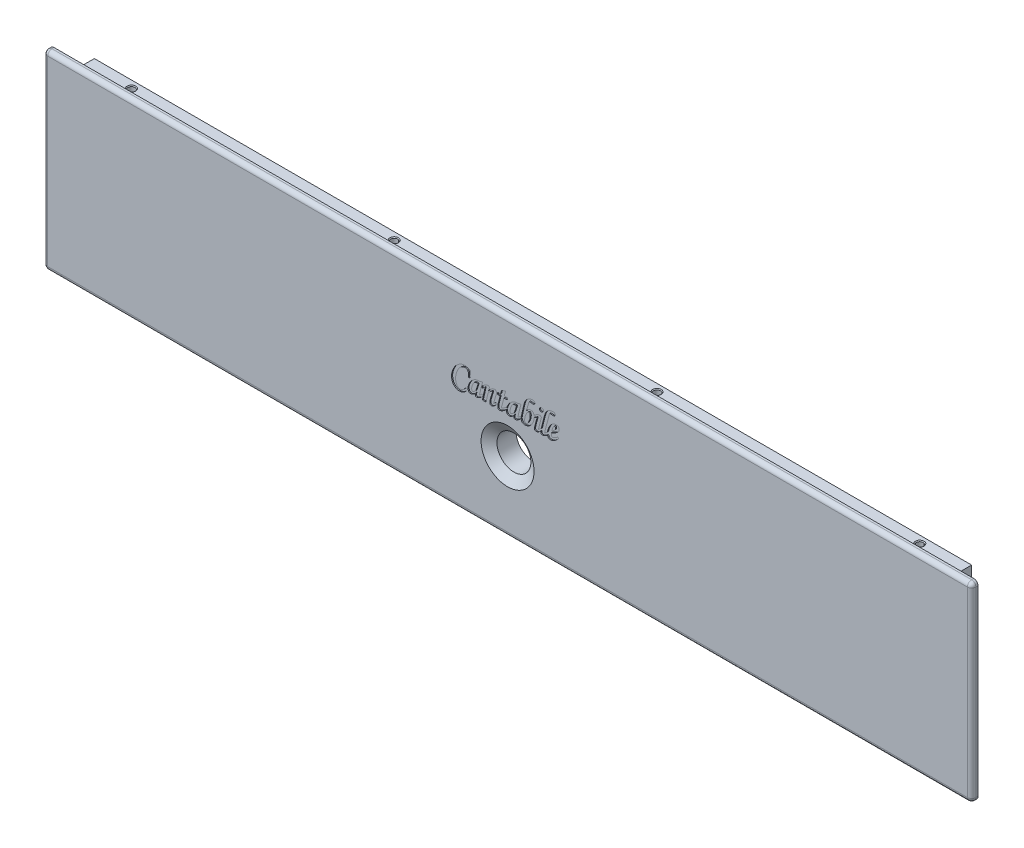
SolidWorks part; units mm, degrees
material "3.3523 (EN-AW 5052)"
ref_plane "前基準面" through (0, 0, 0) normal (0, 0, 1) x (1, 0, 0)
ref_plane "上基準面" through (0, 0, 0) normal (0, 1, 0) x (1, 0, 0)
ref_plane "右基準面" through (0, 0, 0) normal (1, 0, 0) x (0, 0, -1)
sketch "草圖1" plane through (0, 0, 0) normal (0, 0, 1) x (1, 0, 0)
  line L1 (0, 0) -> (438, 0)
  line L2 (0, 0) -> (0, 90)
  line L3 (0, 90) -> (438, 90)
  line L4 (438, 0) -> (438, 90)
  dimension "D1" = 438
  dimension "D2" = 90
extrude "填料-伸長1" add sketch "草圖1" along normal blind 12
sketch "草圖3" plane through (438, 0, 0) normal (1, 0, 0) x (0, 0, -1)
  line L1 (0, 90) -> (-9, 90)
  line L2 (0, 90) -> (0, 86)
  line L3 (0, 86) -> (-9, 86)
  line L4 (-9, 90) -> (-9, 86)
  line L5 (0, 0) -> (-9, 0)
  line L6 (0, 0) -> (0, 4)
  line L7 (0, 4) -> (-9, 4)
  line L8 (-9, 0) -> (-9, 4)
  dimension "D1" = 4
  dimension "D2" = 9
  dimension "D3" = 9
  dimension "D4" = 4
extrude "除料-伸長1" cut sketch "草圖3" against normal through all
hole_wizard "M1.6 錐坑平頭螺釘的錐孔1" positions "草圖9" profile "草圖10" countersink size "M1.6" standard "ISO" end condition through all
sketch "草圖9" plane through (0, 0, 12) normal (0, 0, 1) x (1, 0, 0)
  line L0 (438, 0) -> (438, 90) construction
  line L1 (0, 45) -> (438, 45) construction
  line L2 (0, 90) -> (0, 0) construction
  line L4 (0, 0) -> (438, 0) construction
  point P0 (219, 33)
  dimension "D1" = 219
  dimension "D2" = 33
sketch "草圖10" plane through (219, 33, 12) normal (1, 0, 0) x (0, -1, 0)
  line L0 (0, 0) -> (0, 12)
  line L1 (0, 12) -> (8, 12)
  line L2 (8, 12) -> (8, 3)
  line L3 (8, 3) -> (12.5, 0)
  line L5 (12.5, 0) -> (0, 0)
  line L6 (-8, 3) -> (-12.5, 0) construction
  line L11 (0, -6.35) -> (0, 107.95) construction
  dimension "貫穿孔直徑" = 16
  dimension "貫穿孔深度" = 12
  dimension "近端錐孔直徑" = 25
  dimension "近端錐孔角度" = 112.62
sketch "草圖12" plane through (0, 86, 0) normal (0, 1, 0) x (1, 0, 0)
  line L0 (0, -9) -> (438, -9) construction
  line L1 (438, 0) -> (426, 0)
  line L2 (438, 0) -> (438, -9)
  line L3 (438, -9) -> (426, -9)
  line L4 (426, 0) -> (426, -9)
  line L6 (0, 0) -> (12, 0)
  line L7 (0, 0) -> (0, -9)
  line L8 (0, -9) -> (12, -9)
  line L9 (12, 0) -> (12, -9)
  dimension "D1" = 12
  dimension "D2" = 12
extrude "除料-伸長2" cut sketch "草圖12" against normal through all
fillet "圓角1" radius 2 4 edges at (0, 90, 10.5) (0, 0, 10.5) (438, 0, 10.5) (438, 90, 10.5)
fillet "圓角2" radius 2 8 edges at (0.5858, 89.4142, 12) (219, 90, 12) (437.4142, 89.4142, 12) (438, 45, 12) (437.4142, 0.5858, 12) (219, 0, 12) (0.5858, 0.5858, 12) (0, 45, 12)
hole_wizard "M4 螺紋孔1" positions "草圖13" profile "草圖14" tap size "M4" standard "ISO" end condition through all
sketch "草圖13" plane through (0, 86, 0) normal (0, 1, 0) x (1, 0, 0)
  line L0 (426, -4.5) -> (12, -4.5) construction
  line L1 (426, 0) -> (426, -9) construction
  line L2 (12, -9) -> (12, 0) construction
  point P0 (405, -3.5)
  point P2 (281, -3.5)
  point P4 (157, -3.5)
  point P6 (33, -3.5)
  dimension "D1" = 1
  dimension "D2" = 21
  dimension "D3" = 124
  dimension "D4" = 124
  dimension "D5" = 124
cosmetic thread "鑽孔螺紋17" parameters "D2"=4
cosmetic thread "鑽孔螺紋18" parameters "D2"=4
cosmetic thread "鑽孔螺紋19" parameters "D2"=4
cosmetic thread "鑽孔螺紋20" parameters "D2"=4
sketch "草圖14" plane through (405, 86, 3.5) normal (1, 0, 0) x (0, 0, 1)
  line L0 (0, 0) -> (0, 86)
  line L1 (0, 86) -> (1.65, 86)
  line L2 (1.65, 86) -> (1.65, 0.375)
  line L3 (1.65, 0.375) -> (2.025, 0)
  line L5 (2.025, 0) -> (0, 0)
  line L6 (-1.65, 0.375) -> (-2.025, 0) construction
  line L11 (0, -6.35) -> (0, 107.95) construction
  dimension "貫穿螺孔鑽直徑" = 3.3
  dimension "貫穿螺孔鑽深度" = 86
  dimension "近端錐孔直徑" = 4.05
  dimension "近端錐孔角度" = 90
hole_wizard "M4 螺紋孔3" positions "草圖17" profile "草圖18" tap size "M4" standard "ISO"
sketch "草圖17" plane through (12, 0, 0) normal (-1, 0, 0) x (0, 0, 1)
  line L0 (9, 86) -> (0, 86) construction
  line L1 (9, 4) -> (0, 4) construction
  line L2 (4.5, 86) -> (4.5, 4) construction
  point P0 (3.5, 70)
  point P2 (3.5, 20)
  dimension "D1" = 16
  dimension "D2" = 16
  dimension "D3" = 1
sketch "草圖18" plane through (12, 70, 3.5) normal (0, 1, 0) x (0, 0, 1)
  line L0 (0, 0) -> (0, 8.0914)
  line L1 (0, 8.0914) -> (1.65, 7.1)
  line L2 (1.65, 7.1) -> (1.65, 0.375)
  line L3 (1.65, 0.375) -> (2.025, 0)
  line L5 (2.025, 0) -> (0, 0)
  line L6 (-1.65, 0.375) -> (-2.025, 0) construction
  line L10 (0, 8.0914) -> (-1.65, 7.1) construction
  line L11 (0, -6.35) -> (0, 107.95) construction
  dimension "螺孔鑽直徑" = 3.3
  dimension "螺孔鑽深度" = 7.1
  dimension "近端錐孔直徑" = 4.05
  dimension "近端錐孔角度" = 90
  dimension "導頭角度" = 118
cosmetic thread "鑽孔螺紋9" parameters "D1"=5, "D2"=4
cosmetic thread "鑽孔螺紋10" parameters "D1"=5, "D2"=4
hole_wizard "M4 螺紋孔4" positions "草圖19" profile "草圖20" tap size "M4" standard "ISO"
sketch "草圖19" plane through (426, 0, 0) normal (1, 0, 0) x (0, 0, -1)
  line L0 (-4.5, 4) -> (-4.5, 86) construction
  line L1 (0, 4) -> (-9, 4) construction
  line L2 (0, 86) -> (-9, 86) construction
  point P0 (-3.5, 20)
  point P2 (-3.5, 70)
  dimension "D1" = 1
  dimension "D2" = 16
  dimension "D3" = 16
sketch "草圖20" plane through (426, 20, 3.5) normal (0, 1, 0) x (0, 0, -1)
  line L0 (0, 0) -> (0, 8.0914)
  line L1 (0, 8.0914) -> (1.65, 7.1)
  line L2 (1.65, 7.1) -> (1.65, 0.375)
  line L3 (1.65, 0.375) -> (2.025, 0)
  line L5 (2.025, 0) -> (0, 0)
  line L6 (-1.65, 0.375) -> (-2.025, 0) construction
  line L10 (0, 8.0914) -> (-1.65, 7.1) construction
  line L11 (0, -6.35) -> (0, 107.95) construction
  dimension "螺孔鑽直徑" = 3.3
  dimension "螺孔鑽深度" = 7.1
  dimension "近端錐孔直徑" = 4.05
  dimension "近端錐孔角度" = 90
  dimension "導頭角度" = 118
cosmetic thread "鑽孔螺紋11" parameters "D1"=5, "D2"=4
cosmetic thread "鑽孔螺紋12" parameters "D1"=5, "D2"=4
sketch "草圖22" plane through (0, 0, 12) normal (0, 0, 1) x (1, 0, 0)
  line L0 (194, 50) -> (244, 50)
  line L1 (219, 90) -> (219, 0) construction
  line L2 (438, 90) -> (0, 90) construction
  line L3 (0, 0) -> (438, 0) construction
  point P8 (219, 50)
  dimension "D1" = 50
  dimension "D2" = 40
sketch "草圖23" plane through (0, 0, 12) normal (0, 0, 1) x (1, 0, 0)
  line L0 (201.3049, 56.0288) -> (200.5191, 56.0288)
  line L1 (206.1593, 57.1963) -> (207.1831, 57.2781)
  line L2 (207.1831, 57.2781) -> (206.5807, 55.0645)
  line L3 (206.9897, 52.3798) -> (207.4632, 51.7303)
  line L4 (203.8613, 50.7858) -> (204.1811, 51.6584)
  line L5 (205.9783, 56.946) -> (206.1593, 57.1963)
  line L6 (204.4116, 53.3986) -> (205.0809, 55.6594)
  line L7 (207.0895, 54.7595) -> (206.7821, 55.4363)
  line L8 (210.3443, 56.594) -> (209.9774, 55.1239)
  line L9 (213.7925, 52.3798) -> (214.09, 51.7353)
  line L10 (209.5015, 53.0144) -> (208.8446, 50)
  line L11 (208.8446, 50) -> (207.1093, 50)
  line L12 (207.6795, 52.5706) -> (208.3711, 55.7214)
  line L13 (216.1332, 58.4432) -> (218.0519, 59.1175)
  line L14 (218.0519, 59.1175) -> (217.4421, 56.822)
  line L15 (217.4421, 56.822) -> (218.9716, 56.822)
  line L16 (218.9716, 56.822) -> (218.808, 55.8701)
  line L17 (218.808, 55.8701) -> (217.2587, 55.8701)
  line L18 (217.2587, 55.8701) -> (216.5695, 53.1829)
  line L19 (218.3866, 52.6971) -> (218.5861, 52.4473)
  line L20 (214.6806, 52.7814) -> (215.5209, 55.8701)
  line L21 (215.5209, 55.8701) -> (214.1898, 55.8701)
  line L22 (214.1898, 55.8701) -> (214.3707, 56.822)
  line L23 (214.3707, 56.822) -> (215.7093, 56.822)
  line L24 (215.7093, 56.822) -> (216.1332, 58.4432)
  line L25 (224.2945, 57.1963) -> (225.3183, 57.2781)
  line L26 (225.3183, 57.2781) -> (224.7159, 55.0645)
  line L27 (225.1249, 52.3798) -> (225.4225, 51.9716)
  line L28 (221.9965, 50.7858) -> (222.3163, 51.6584)
  line L29 (224.1135, 56.946) -> (224.2945, 57.1963)
  line L30 (222.5469, 53.3986) -> (223.2162, 55.6594)
  line L31 (225.6337, 53.2127) -> (226.6204, 57.5483)
  line L32 (228.6233, 58.5597) -> (227.8375, 55.8825)
  line L33 (231.621, 55.0768) -> (231.587, 55.0938)
  line L34 (234.8089, 52.3798) -> (234.9242, 52.2458)
  line L36 (235.2012, 53.416) -> (236.0837, 57.0203)
  line L37 (238.0271, 57.2434) -> (237.0951, 53.9539)
  line L38 (242.7774, 52.6971) -> (243.0625, 52.0451)
  spline S0 degree 3 poles (200.5191, 56.0288) (200.5306, 56.2658) (200.5483, 56.6689) (200.5585, 57.0723) (200.5588, 57.2385) knots 0 0 0 0 0.588273 1 1 1 1
  spline S1 degree 3 poles (200.5588, 57.2385) (200.5556, 57.4103) (200.5508, 57.6597) (200.4981, 57.9739) (200.4489, 58.1778) (200.389, 58.3615) (200.3076, 58.5207) (200.2174, 58.6622) (200.0737, 58.8156) (199.8707, 58.9729) (199.4911, 59.1539) (199.1724, 59.2017) (198.9574, 59.2018) knots 0 0 0 0 0.178113 0.256952 0.329103 0.395064 0.45623 0.513606 0.568061 0.672874 0.777251 1 1 1 1
  spline S2 degree 3 poles (198.9574, 59.2018) (198.8066, 59.2009) (198.5775, 59.1751) (198.2739, 59.1008) (198.0394, 59.0165) (197.7992, 58.9124) (197.5532, 58.7863) (197.3057, 58.6328) (197.0522, 58.4612) (196.8022, 58.2603) (196.5591, 58.0311) (196.3218, 57.7745) (196.0954, 57.4862) (195.8746, 57.1708) (195.661, 56.8275) (195.4556, 56.4548) (195.2597, 56.0581) (195.0792, 55.6452) (194.9241, 55.2232) (194.7887, 54.7986) (194.6797, 54.369) (194.5952, 53.9353) (194.5165, 53.3506) (194.4895, 52.9085) (194.4903, 52.6128) knots 0 0 0 0 0.052157 0.079581 0.1081 0.138359 0.170238 0.20377 0.239183 0.276245 0.314724 0.354835 0.397217 0.441611 0.488159 0.537233 0.588954 0.64139 0.693289 0.744623 0.795723 0.846755 0.897604 1 1 1 1
  spline S3 degree 3 poles (194.4903, 52.6128) (194.4901, 52.3447) (194.5072, 51.9545) (194.5739, 51.4555) (194.6437, 51.1209) (194.7311, 50.8123) (194.843, 50.5322) (194.9724, 50.2784) (195.1208, 50.0526) (195.2848, 49.8557) (195.4542, 49.6825) (195.6302, 49.5348) (195.8142, 49.4151) (196.005, 49.3222) (196.2672, 49.2317) (196.4745, 49.2056) (196.6123, 49.2067) knots 0 0 0 0 0.180488 0.26245 0.338589 0.410404 0.478053 0.541236 0.601861 0.659544 0.713425 0.76477 0.813828 0.860841 0.907276 1 1 1 1
  spline S4 degree 3 poles (196.6123, 49.2067) (196.8359, 49.2025) (197.1714, 49.2633) (197.5985, 49.4338) (197.9116, 49.6221) (198.221, 49.8563) (198.6376, 50.2574) (198.9164, 50.6108) (199.0912, 50.8676) knots 0 0 0 0 0.214884 0.325896 0.442526 0.566721 0.699958 1 1 1 1
  spline S5 degree 3 poles (199.0912, 50.8676) (199.1429, 50.9345) (199.2454, 51.0625) (199.4024, 51.1102) (199.473, 51.1106) knots 0 0 0 0 0.550225 1 1 1 1
  spline S6 degree 3 poles (199.473, 51.1106) (199.5555, 51.1137) (199.6727, 51.0962) (199.8142, 51.0384) (199.8937, 50.9756) (199.9563, 50.9093) (200.0179, 50.8336) (200.0411, 50.7693) (200.0431, 50.7288) knots 0 0 0 0 0.330207 0.471562 0.609117 0.733657 0.837988 1 1 1 1
  spline S7 degree 3 poles (200.0431, 50.7288) (200.0394, 50.6802) (200.0187, 50.5997) (199.9603, 50.4912) (199.9001, 50.3845) (199.8165, 50.2675) (199.7198, 50.134) (199.6022, 49.9891) (199.4253, 49.7728) (199.1704, 49.5068) (198.8268, 49.2091) (198.44, 48.9421) (198.0217, 48.7043) (197.5826, 48.5069) (196.9916, 48.3132) (196.5326, 48.2572) (196.2305, 48.2548) knots 0 0 0 0 0.030514 0.051373 0.07715 0.107337 0.141439 0.180532 0.224326 0.316699 0.411135 0.509039 0.610924 0.712533 0.810541 1 1 1 1
  spline S8 degree 3 poles (196.2305, 48.2548) (195.9058, 48.2524) (195.4201, 48.3197) (194.8071, 48.541) (194.3714, 48.7708) (193.9705, 49.0636) (193.6105, 49.4118) (193.3027, 49.8184) (193.0856, 50.1958) (192.9436, 50.5237) (192.8446, 50.7815) (192.7679, 51.0527) (192.6985, 51.3332) (192.6512, 51.6269) (192.5997, 52.0386) (192.5869, 52.3548) (192.5865, 52.5682) knots 0 0 0 0 0.153719 0.229891 0.307833 0.386308 0.464392 0.544273 0.627223 0.670001 0.713491 0.757971 0.803462 0.850324 0.898842 1 1 1 1
  spline S9 degree 3 poles (192.5865, 52.5682) (192.5853, 52.8733) (192.619, 53.3316) (192.7124, 53.9397) (192.8187, 54.3951) (192.9489, 54.8513) (193.1149, 55.3044) (193.3046, 55.7588) (193.5251, 56.2063) (193.7649, 56.6425) (194.0265, 57.0555) (194.2974, 57.4472) (194.5894, 57.8082) (194.8916, 58.1481) (195.2114, 58.4593) (195.5449, 58.747) (195.8934, 59.005) (196.2476, 59.2371) (196.6033, 59.4381) (196.9557, 59.6115) (197.3086, 59.7497) (197.6585, 59.8606) (198.1203, 59.9621) (198.47, 59.9967) (198.702, 59.995) knots 0 0 0 0 0.086975 0.130883 0.175372 0.220281 0.266138 0.312938 0.360694 0.408385 0.454884 0.500072 0.544175 0.587241 0.629748 0.671371 0.712811 0.753347 0.792087 0.829302 0.865283 0.900101 0.933901 1 1 1 1
  spline S10 degree 2 poles (198.702, 59.995) (199.2243, 59.9983) (199.7283, 59.8612) knots 0 0 0 1 1 1
  spline S11 degree 3 poles (199.7283, 59.8612) (199.803, 59.8365) (199.9365, 59.792) (200.1396, 59.711) (200.3572, 59.6288) (200.6154, 59.5234) (201.0437, 59.3452) (201.3881, 59.2068) (201.6296, 59.1026) knots 0 0 0 0 0.115252 0.206088 0.320307 0.456102 0.614615 1 1 1 1
  spline S12 degree 3 poles (201.6296, 59.1026) (201.5305, 58.6092) (201.3786, 57.5877) (201.3183, 56.5569) (201.3049, 56.0288) knots 0 0 0 0 0.487837 1 1 1 1
  spline S13 degree 3 poles (206.5807, 55.0645) (206.4569, 54.6411) (206.2209, 53.7283) (206.019, 52.8074) (205.9213, 52.3153) knots 0 0 0 0 0.467807 1 1 1 1
  spline S14 degree 3 poles (205.9213, 52.3153) (205.8727, 52.0936) (205.8227, 51.7936) (205.7714, 51.4653) (205.7624, 51.3605) (205.7606, 51.333) knots 0 0 0 0 0.631671 0.84781 0.924694 0.924694 0.924694 0.924694
  spline S15 degree 3 poles (212.4516, 51.1821) (212.4712, 51.1978) (212.6149, 51.3279) (212.7369, 51.471) (212.8456, 51.5989) knots 0.22546 0.22546 0.22546 0.22546 0.326776 1 1 1 1
  spline S16 degree 3 poles (233.617, 51.1922) (233.6575, 51.2237) (233.7499, 51.2988) (233.8995, 51.4391) (234.0828, 51.6176) (234.3934, 51.932) (234.6354, 52.1939) (234.8089, 52.3798) knots 0.092392 0.092392 0.092392 0.092392 0.174868 0.285512 0.423469 0.588815 1 1 1 1
  spline S17 degree 3 poles (205.9039, 51.4403) (206.0715, 51.5728) (206.439, 51.8797) (206.7954, 52.1994) (206.9897, 52.3798) knots 0 0 0 0 0.446233 1 1 1 1
  spline S18 degree 3 poles (207.4632, 51.7303) (207.3135, 51.5892) (207.104, 51.3819) (206.8286, 51.1304) (206.6556, 50.9693) (206.4985, 50.8351) (206.3352, 50.6892) (206.2165, 50.5977) (206.1444, 50.5429) knots 0 0 0 0 0.347601 0.49778 0.630204 0.746966 0.846918 1 1 1 1
  spline S19 degree 3 poles (206.1444, 50.5429) (205.9819, 50.4244) (205.638, 50.2131) (205.2733, 50.0398) (205.0834, 49.9703) knots 0 0 0 0 0.498684 1 1 1 1
  spline S20 degree 2 poles (205.0834, 49.9703) (204.74, 49.8386) (204.372, 49.8413) knots 0 0 0 1 1 1
  spline S21 degree 3 poles (204.372, 49.8413) (204.2894, 49.842) (204.1685, 49.8562) (204.0269, 49.9193) (203.9395, 49.9819) (203.8732, 50.0649) (203.8049, 50.1999) (203.7944, 50.3179) (203.7919, 50.3966) knots 0 0 0 0 0.272866 0.392021 0.506662 0.622488 0.7379 1 1 1 1
  spline S22 degree 2 poles (203.7919, 50.3966) (203.7998, 50.5958) (203.8613, 50.7858) knots 0 0 0 1 1 1
  spline S23 degree 3 poles (204.1811, 51.6584) (204.1307, 51.5271) (204.0309, 51.3341) (203.8534, 51.0983) (203.6967, 50.9177) (203.512, 50.7436) (203.228, 50.5026) (202.9882, 50.3422) (202.8202, 50.238) knots 0 0 0 0 0.210843 0.32332 0.441828 0.56886 0.703355 1 1 1 1
  spline S24 degree 3 poles (202.8202, 50.238) (202.6223, 50.115) (202.2176, 49.9153) (201.7719, 49.8409) (201.5584, 49.8413) knots 0 0 0 0 0.522665 1 1 1 1
  spline S25 degree 3 poles (201.5584, 49.8413) (201.3914, 49.8409) (201.0604, 49.896) (200.7946, 50.1029) (200.7007, 50.2305) knots 0 0 0 0 0.515349 1 1 1 1
  spline S26 degree 3 poles (200.7007, 50.2305) (200.5734, 50.3952) (200.3698, 50.7986) (200.3276, 51.2479) (200.3239, 51.4824) knots 0 0 0 0 0.468568 1 1 1 1
  spline S27 degree 3 poles (200.3239, 51.4824) (200.3233, 51.7971) (200.3953, 52.2821) (200.5851, 52.9312) (200.7939, 53.4472) (201.0471, 53.9638) (201.3464, 54.4616) (201.6845, 54.9343) (202.0586, 55.3758) (202.4551, 55.7813) (202.9998, 56.2385) (203.4421, 56.5162) (203.7498, 56.6584) knots 0 0 0 0 0.145247 0.225743 0.312613 0.402594 0.491809 0.581186 0.671302 0.759479 0.843374 1 1 1 1
  spline S28 degree 3 poles (203.7498, 56.6584) (204.002, 56.7747) (204.5867, 56.9428) (205.1931, 56.9799) (205.5197, 56.9807) knots 0 0 0 0 0.458723 1 1 1 1
  spline S29 degree 2 poles (205.5197, 56.9807) (205.7505, 56.9822) (205.9783, 56.946) knots 0 0 0 1 1 1
  spline S30 degree 2 poles (205.0809, 55.6594) (204.7932, 55.7112) (204.5009, 55.7115) knots 0 0 0 1 1 1
  spline S31 degree 3 poles (204.5009, 55.7115) (204.3123, 55.7132) (204.03, 55.673) (203.6815, 55.5316) (203.4786, 55.4103) (203.3226, 55.29) (203.2096, 55.1729) (203.0934, 55.0406) (202.978, 54.8861) (202.8633, 54.7121) (202.7491, 54.5173) (202.6347, 54.3032) (202.485, 53.994) (202.3205, 53.5924) (202.1268, 52.9414) (202.0721, 52.4385) (202.069, 52.1071) knots 0 0 0 0 0.118489 0.176751 0.235458 0.26653 0.300322 0.337509 0.377195 0.421425 0.468463 0.519124 0.573953 0.6844 0.791573 1 1 1 1
  spline S32 degree 3 poles (202.069, 52.1071) (202.0678, 51.9627) (202.0778, 51.7667) (202.1309, 51.5372) (202.1875, 51.4289) (202.2517, 51.3581) (202.3266, 51.2988) (202.3851, 51.2681) (202.426, 51.2692) knots 0 0 0 0 0.43794 0.593618 0.710269 0.804374 0.881115 1 1 1 1
  spline S33 degree 3 poles (202.426, 51.2692) (202.6096, 51.2699) (202.8924, 51.3593) (203.249, 51.5765) (203.4847, 51.7685) (203.6737, 51.9515) (203.8082, 52.1129) (203.9342, 52.2885) (204.0513, 52.4793) (204.155, 52.6876) (204.2868, 52.9908) (204.3655, 53.2324) (204.4116, 53.3986) knots 0 0 0 0 0.175898 0.282287 0.403702 0.470012 0.537126 0.60719 0.679492 0.754047 0.832661 1 1 1 1
  spline S34 degree 3 poles (206.7821, 55.4363) (206.9558, 55.6129) (207.2103, 55.8645) (207.5487, 56.1756) (207.7771, 56.3754) (207.9921, 56.5508) (208.1929, 56.7023) (208.3788, 56.8313) (208.604, 56.9644) (208.8656, 57.0938) (209.2422, 57.2426) (209.5251, 57.2968) (209.7048, 57.298) knots 0 0 0 0 0.209677 0.302723 0.388966 0.466509 0.537417 0.601813 0.65794 0.75864 0.84851 1 1 1 1
  spline S35 degree 3 poles (209.7048, 57.298) (209.8023, 57.3024) (209.9402, 57.2821) (210.1109, 57.2275) (210.2092, 57.1626) (210.2895, 57.0962) (210.3631, 57.012) (210.396, 56.9415) (210.3964, 56.8939) knots 0 0 0 0 0.33478 0.480259 0.615021 0.738664 0.839994 1 1 1 1
  spline S36 degree 3 poles (210.3964, 56.8939) (210.3962, 56.858) (210.38, 56.7574) (210.3573, 56.6585) (210.3443, 56.594) knots 0 0 0 0 0.352433 1 1 1 1
  spline S37 degree 3 poles (209.9774, 55.1239) (210.0442, 55.2813) (210.1793, 55.5069) (210.3975, 55.7924) (210.5901, 56.0107) (210.8135, 56.2227) (211.1495, 56.5186) (211.436, 56.7131) (211.6309, 56.8468) knots 0 0 0 0 0.211405 0.324738 0.445234 0.572051 0.706426 1 1 1 1
  spline S38 degree 3 poles (211.6309, 56.8468) (211.8357, 56.977) (212.2074, 57.1906) (212.6245, 57.2978) (212.8084, 57.298) knots 0 0 0 0 0.571537 1 1 1 1
  spline S39 degree 3 poles (212.8084, 57.298) (212.9581, 57.3011) (213.1748, 57.2702) (213.4232, 57.1401) (213.5594, 57.0049) (213.6631, 56.8472) (213.7664, 56.611) (213.7921, 56.4154) (213.7925, 56.2841) knots 0 0 0 0 0.281055 0.400985 0.519314 0.636614 0.753175 1 1 1 1
  spline S40 degree 2 poles (213.7925, 56.2841) (213.7826, 55.9722) (213.7058, 55.6693) knots 0 0 0 1 1 1
  spline S41 degree 3 poles (213.7058, 55.6693) (213.6739, 55.5672) (213.6238, 55.3893) (213.5395, 55.1232) (213.4553, 54.854) (213.3601, 54.5382) (213.1951, 54.029) (213.074, 53.6211) (212.9794, 53.3366) knots 0 0 0 0 0.131297 0.226931 0.342781 0.477579 0.631926 1 1 1 1
  spline S42 degree 3 poles (212.9794, 53.3366) (212.8983, 53.0901) (212.7891, 52.7353) (212.6593, 52.2833) (212.5839, 51.995) (212.5271, 51.7393) (212.4752, 51.4733) (212.453, 51.2904) (212.4516, 51.1821) knots 0 0 0 0 0.34671 0.495908 0.628166 0.744662 0.845764 0.990231 0.990231 0.990231 0.990231
  spline S43 degree 3 poles (234.9242, 52.2458) (234.9417, 52.3253) (235.0309, 52.7161) (235.1241, 53.1059) (235.2012, 53.416) knots 0.56418 0.56418 0.56418 0.56418 0.652637 1 1 1 1
  spline S45 degree 3 poles (212.8456, 51.5989) (212.9662, 51.738) (213.2599, 52.0277) (213.6033, 52.2562) (213.7925, 52.3798) knots 0 0 0 0 0.448625 1 1 1 1
  spline S46 degree 3 poles (214.09, 51.7353) (213.8362, 51.4353) (213.3124, 50.8838) (212.717, 50.4102) (212.4118, 50.2082) knots 0 0 0 0 0.517913 1 1 1 1
  spline S47 degree 3 poles (212.4118, 50.2082) (212.2482, 50.0967) (211.9262, 49.9206) (211.567, 49.8398) (211.4003, 49.8413) knots 0 0 0 0 0.544887 1 1 1 1
  spline S48 degree 3 poles (211.4003, 49.8413) (211.2863, 49.8446) (211.1118, 49.8658) (210.9204, 49.9838) (210.7998, 50.0973) (210.7071, 50.2486) (210.6178, 50.5128) (210.5986, 50.7344) (210.5997, 50.8899) knots 0 0 0 0 0.231554 0.337567 0.445116 0.560222 0.688303 1 1 1 1
  spline S49 degree 3 poles (210.5997, 50.8899) (210.6027, 50.9644) (210.6082, 51.085) (210.635, 51.2563) (210.6622, 51.4099) (210.694, 51.5814) (210.7373, 51.7686) (210.7854, 51.9741) (210.8472, 52.1946) (210.9104, 52.4331) (210.983, 52.6882) (211.0614, 52.9615) (211.1521, 53.2497) (211.2448, 53.5564) (211.3901, 53.9967) (211.4959, 54.3379) (211.5764, 54.5687) knots 0 0 0 0 0.058623 0.094739 0.136298 0.181286 0.231893 0.287372 0.347272 0.411902 0.481437 0.55588 0.635427 0.719083 0.807859 1 1 1 1
  spline S50 degree 3 poles (211.5764, 54.5687) (211.6208, 54.7203) (211.6821, 54.9338) (211.7517, 55.2018) (211.7965, 55.3594) (211.8237, 55.4928) (211.8551, 55.6128) (211.8656, 55.6914) (211.8689, 55.7338) knots 0 0 0 0 0.394215 0.554245 0.690769 0.802804 0.893822 1 1 1 1
  spline S51 degree 3 poles (211.8689, 55.7338) (211.8719, 55.7693) (211.8511, 55.8469) (211.7753, 55.8752) (211.74, 55.8701) knots 0 0 0 0 0.507504 1 1 1 1
  spline S52 degree 3 poles (211.74, 55.8701) (211.6531, 55.8645) (211.4331, 55.7706) (211.2404, 55.6341) (211.1153, 55.5503) knots 0 0 0 0 0.362826 1 1 1 1
  spline S53 degree 3 poles (211.1153, 55.5503) (210.9017, 55.3964) (210.4814, 55.0418) (210.1403, 54.6104) (209.975, 54.3803) knots 0 0 0 0 0.481397 1 1 1 1
  spline S54 degree 3 poles (209.975, 54.3803) (209.9248, 54.3106) (209.8611, 54.1889) (209.7827, 54.0111) (209.7237, 53.8495) (209.6674, 53.6679) (209.5887, 53.3887) (209.5329, 53.1686) (209.5015, 53.0144) knots 0 0 0 0 0.176645 0.282815 0.401006 0.531561 0.675189 1 1 1 1
  spline S55 degree 3 poles (207.1093, 50) (207.212, 50.4536) (207.4081, 51.3091) (207.5931, 52.1672) (207.6795, 52.5706) knots 0 0 0 0 0.529867 1 1 1 1
  spline S56 degree 2 poles (208.3711, 55.7214) (208.4022, 55.8411) (208.4108, 55.9643) knots 0 0 0 1 1 1
  spline S57 degree 3 poles (208.4108, 55.9643) (208.4161, 55.9765) (208.4147, 55.9983) (208.4106, 56.0143) knots 0 0 0 0 0.766733 0.766733 0.766733 0.766733
  spline S58 degree 3 poles (208.4106, 56.0143) (208.4093, 56.0032) (208.3322, 55.9435) (208.3108, 55.8886) (208.2422, 55.8453) knots 0.061745 0.061745 0.061745 0.061745 0.212651 1 1 1 1
  spline S59 degree 3 poles (208.2422, 55.8453) (208.0731, 55.6992) (207.6805, 55.3459) (207.3059, 54.9736) (207.0895, 54.7595) knots 0 0 0 0 0.423354 1 1 1 1
  spline S60 degree 3 poles (216.5695, 53.1829) (216.5019, 53.0025) (216.4198, 52.7385) (216.3119, 52.4045) (216.2565, 52.186) (216.2073, 51.9917) (216.168, 51.7761) (216.1491, 51.6252) (216.1481, 51.532) knots 0 0 0 0 0.337957 0.485177 0.615659 0.733474 0.836707 1 1 1 1
  spline S61 degree 3 poles (216.1481, 51.532) (216.1503, 51.4773) (216.149, 51.407) (216.1615, 51.3257) (216.1696, 51.2925) (216.1754, 51.273) (216.1828, 51.2692) knots 0 0 0 0 0.610351 0.788013 0.911533 1 1 1 1
  spline S62 degree 3 poles (216.1828, 51.2692) (216.2815, 51.2725) (216.523, 51.3687) (216.7399, 51.5059) (216.872, 51.5964) knots 0 0 0 0 0.377761 1 1 1 1
  spline S63 degree 3 poles (216.872, 51.5964) (217.1132, 51.7643) (217.6229, 52.1248) (218.1217, 52.4999) (218.3866, 52.6971) knots 0 0 0 0 0.470951 1 1 1 1
  spline S64 degree 3 poles (218.4658, 51.6978) (218.4617, 51.6946) (218.3201, 51.5841) (218.0535, 51.3779) (217.6766, 51.0929) (217.3382, 50.8416) (217.0353, 50.6293) (216.7734, 50.449) (216.5475, 50.307) (216.3036, 50.168) (216.0334, 50.0402) (215.6523, 49.8993) (215.3695, 49.8417) (215.1888, 49.8413) knots 0.12814 0.12814 0.12814 0.12814 0.131703 0.251054 0.358855 0.455121 0.539543 0.612017 0.672748 0.722136 0.804106 0.876926 1 1 1 1
  spline S65 degree 3 poles (215.1888, 49.8413) (215.0726, 49.8422) (214.8979, 49.87) (214.7, 49.9878) (214.5784, 50.1104) (214.4831, 50.2684) (214.3895, 50.5455) (214.3681, 50.778) (214.3707, 50.942) knots 0 0 0 0 0.225189 0.330932 0.439083 0.55494 0.683439 1 1 1 1
  spline S66 degree 3 poles (214.3707, 50.942) (214.3712, 51.0579) (214.3826, 51.2412) (214.416, 51.4967) (214.4466, 51.7179) (214.4934, 51.957) (214.5634, 52.3156) (214.6352, 52.5905) (214.6806, 52.7814) knots 0 0 0 0 0.186027 0.294262 0.413544 0.544379 0.685085 1 1 1 1
  spline S67 degree 3 poles (224.7159, 55.0645) (224.5922, 54.6411) (224.3561, 53.7283) (224.1542, 52.8074) (224.0565, 52.3153) knots 0 0 0 0 0.467807 1 1 1 1
  spline S68 degree 3 poles (224.0565, 52.3153) (224.0079, 52.0936) (223.9579, 51.7936) (223.9066, 51.4653) (223.8976, 51.3605) (223.8959, 51.333) knots 0 0 0 0 0.631671 0.84781 0.924694 0.924694 0.924694 0.924694
  spline S69 degree 3 poles (205.7606, 51.333) (205.81, 51.3666) (205.857, 51.4027) (205.9039, 51.4403) knots 0.455857 0.455857 0.455857 0.455857 1 1 1 1
  spline S71 degree 3 poles (224.0392, 51.4403) (224.2067, 51.5728) (224.5742, 51.8797) (224.9306, 52.1994) (225.1249, 52.3798) knots 0 0 0 0 0.446233 1 1 1 1
  spline S72 degree 3 poles (225.403, 51.5434) (225.3904, 51.5313) (225.3072, 51.4511) (225.1598, 51.3094) (224.9638, 51.1304) (224.7908, 50.9693) (224.6337, 50.8351) (224.4705, 50.6892) (224.3517, 50.5977) (224.2796, 50.5429) knots 0.152317 0.152317 0.152317 0.152317 0.181697 0.347601 0.49778 0.630204 0.746966 0.846918 1 1 1 1
  spline S73 degree 3 poles (224.2796, 50.5429) (224.1171, 50.4244) (223.7732, 50.2131) (223.4086, 50.0398) (223.2186, 49.9703) knots 0 0 0 0 0.498684 1 1 1 1
  spline S74 degree 2 poles (223.2186, 49.9703) (222.8752, 49.8386) (222.5072, 49.8413) knots 0 0 0 1 1 1
  spline S75 degree 3 poles (222.5072, 49.8413) (222.4246, 49.842) (222.3037, 49.8562) (222.1621, 49.9193) (222.0747, 49.9819) (222.0084, 50.0649) (221.9401, 50.1999) (221.9296, 50.3179) (221.9271, 50.3966) knots 0 0 0 0 0.272866 0.392021 0.506662 0.622488 0.7379 1 1 1 1
  spline S76 degree 2 poles (221.9271, 50.3966) (221.9351, 50.5958) (221.9965, 50.7858) knots 0 0 0 1 1 1
  spline S77 degree 3 poles (222.3163, 51.6584) (222.2659, 51.5271) (222.1661, 51.3341) (221.9886, 51.0983) (221.832, 50.9177) (221.6473, 50.7436) (221.3632, 50.5026) (221.1234, 50.3422) (220.9554, 50.238) knots 0 0 0 0 0.210843 0.32332 0.441828 0.56886 0.703355 1 1 1 1
  spline S78 degree 3 poles (220.9554, 50.238) (220.7575, 50.115) (220.3528, 49.9153) (219.9071, 49.8409) (219.6936, 49.8413) knots 0 0 0 0 0.522665 1 1 1 1
  spline S79 degree 3 poles (219.6936, 49.8413) (219.5267, 49.8409) (219.1956, 49.896) (218.9298, 50.1029) (218.8359, 50.2305) knots 0 0 0 0 0.515349 1 1 1 1
  spline S80 degree 3 poles (218.8359, 50.2305) (218.7087, 50.3952) (218.5051, 50.7986) (218.4628, 51.2479) (218.4591, 51.4824) knots 0 0 0 0 0.468568 1 1 1 1
  spline S81 degree 2 poles (218.4591, 51.4824) (218.459, 51.5903) (218.4658, 51.6978) knots 0 0 0 0.033205 0.033205 0.033205
  spline S82 degree 3 poles (221.885, 56.6584) (222.1372, 56.7747) (222.7219, 56.9428) (223.3283, 56.9799) (223.6549, 56.9807) knots 0 0 0 0 0.458723 1 1 1 1
  spline S83 degree 2 poles (223.6549, 56.9807) (223.8858, 56.9822) (224.1135, 56.946) knots 0 0 0 1 1 1
  spline S84 degree 2 poles (223.2162, 55.6594) (222.9284, 55.7112) (222.6361, 55.7115) knots 0 0 0 1 1 1
  spline S85 degree 3 poles (222.6361, 55.7115) (222.4475, 55.7132) (222.1653, 55.673) (221.8167, 55.5316) (221.6138, 55.4103) (221.4578, 55.29) (221.3449, 55.1729) (221.2287, 55.0406) (221.1132, 54.8861) (220.9985, 54.7121) (220.8843, 54.5173) (220.7699, 54.3032) (220.6202, 53.994) (220.4557, 53.5924) (220.262, 52.9414) (220.2073, 52.4385) (220.2043, 52.1071) knots 0 0 0 0 0.118489 0.176751 0.235458 0.26653 0.300322 0.337509 0.377195 0.421425 0.468463 0.519124 0.573953 0.6844 0.791573 1 1 1 1
  spline S86 degree 3 poles (220.2043, 52.1071) (220.203, 51.9627) (220.213, 51.7667) (220.2661, 51.5372) (220.3228, 51.4289) (220.387, 51.3581) (220.4618, 51.2988) (220.5204, 51.2681) (220.5612, 51.2692) knots 0 0 0 0 0.43794 0.593618 0.710269 0.804374 0.881115 1 1 1 1
  spline S87 degree 3 poles (220.5612, 51.2692) (220.7449, 51.2699) (221.0276, 51.3593) (221.3842, 51.5765) (221.6199, 51.7685) (221.8089, 51.9515) (221.9434, 52.1129) (222.0694, 52.2885) (222.1865, 52.4793) (222.2902, 52.6876) (222.422, 52.9908) (222.5007, 53.2324) (222.5469, 53.3986) knots 0 0 0 0 0.175898 0.282287 0.403702 0.470012 0.537126 0.60719 0.679492 0.754047 0.832661 1 1 1 1
  spline S88 degree 3 poles (227.8375, 55.8825) (227.9145, 56.1084) (228.1009, 56.4204) (228.4546, 56.7508) (228.7673, 56.9451) (229.0946, 57.0939) (229.4961, 57.2452) (229.8001, 57.2971) (229.9942, 57.298) knots 0 0 0 0 0.261535 0.392044 0.528917 0.664287 0.787023 1 1 1 1
  spline S89 degree 3 poles (229.9942, 57.298) (230.1178, 57.2986) (230.2994, 57.2852) (230.5292, 57.2271) (230.6849, 57.1681) (230.829, 57.0925) (230.961, 57.0006) (231.0811, 56.8905) (231.224, 56.7186) (231.3773, 56.4679) (231.4851, 56.163) (231.5298, 55.9601) (231.5444, 55.8763) knots 0 0 0 0 0.127476 0.186318 0.243707 0.298539 0.353562 0.408992 0.465778 0.583449 0.709488 0.7971 0.7971 0.7971 0.7971
  spline S90 degree 3 poles (231.587, 55.0938) (231.5854, 55.046) (231.5785, 54.8854) (231.5551, 54.6127) (231.5009, 54.2772) (231.4331, 53.9413) (231.3403, 53.6073) (231.2289, 53.2746) (231.0963, 52.944) (230.9471, 52.6165) (230.7788, 52.2998) (230.6018, 51.9963) (230.4095, 51.7136) (230.2088, 51.447) (229.996, 51.1986) (229.7691, 50.97) (229.5318, 50.7591) (229.284, 50.5692) (229.032, 50.398) (228.7773, 50.2489) (228.5209, 50.1244) (228.2644, 50.023) (228.0086, 49.9391) (227.6662, 49.8635) (227.4052, 49.8441) (227.2326, 49.8413) knots 0.025356 0.025356 0.025356 0.025356 0.044115 0.088382 0.13268 0.177383 0.222769 0.2686 0.315021 0.362464 0.409745 0.455677 0.500281 0.543793 0.586558 0.628514 0.670088 0.71101 0.750938 0.789587 0.82671 0.862655 0.897723 0.932258 1 1 1 1
  spline S91 degree 3 poles (227.2326, 49.8413) (227.101, 49.8425) (226.9066, 49.8527) (226.6586, 49.9075) (226.4873, 49.9626) (226.3243, 50.0289) (226.1722, 50.1129) (226.0338, 50.2173) (225.9019, 50.329) (225.7856, 50.4564) (225.6834, 50.5933) (225.596, 50.7392) (225.5279, 50.895) (225.4677, 51.0561) (225.4334, 51.2294) (225.41, 51.3923) (225.4036, 51.4981) (225.403, 51.5434) knots 0 0 0 0 0.138709 0.20367 0.266623 0.327805 0.38851 0.44884 0.509842 0.570128 0.629759 0.68939 0.748524 0.808459 0.869838 0.933886 0.98145 0.98145 0.98145 0.98145
  spline S92 degree 3 poles (225.4225, 51.9716) (225.4321, 52.0807) (225.4813, 52.498) (225.5663, 52.9098) (225.6337, 53.2127) knots 0.229731 0.229731 0.229731 0.229731 0.430596 1 1 1 1
  spline S93 degree 3 poles (226.6204, 57.5483) (226.675, 57.8034) (226.7689, 58.1717) (226.9109, 58.6438) (227.023, 58.9634) (227.1384, 59.2607) (227.2598, 59.5338) (227.386, 59.7836) (227.5638, 60.0826) (227.8112, 60.4254) (228.1561, 60.7906) (228.5424, 61.1165) (228.9681, 61.3886) (229.4065, 61.6119) (229.9732, 61.8258) (230.4091, 61.8991) (230.6932, 61.8989) knots 0 0 0 0 0.121019 0.176335 0.228726 0.278147 0.324325 0.367371 0.407949 0.485651 0.562969 0.640546 0.719576 0.796921 0.868508 1 1 1 1
  spline S94 degree 3 poles (230.6932, 61.8989) (230.8731, 61.8967) (231.1311, 61.8813) (231.4362, 61.773) (231.6066, 61.6643) (231.7405, 61.5398) (231.8684, 61.3591) (231.9071, 61.1995) (231.9079, 61.0957) knots 0 0 0 0 0.334479 0.471389 0.594411 0.705823 0.808043 1 1 1 1
  spline S95 degree 3 poles (231.9079, 61.0957) (231.9072, 60.9998) (231.8712, 60.8518) (231.7567, 60.6798) (231.641, 60.5533) (231.4924, 60.4427) (231.233, 60.3353) (231.0138, 60.3112) (230.8618, 60.3123) knots 0 0 0 0 0.198089 0.305662 0.424145 0.551256 0.685175 1 1 1 1
  spline S96 degree 3 poles (230.8618, 60.3123) (230.7358, 60.3147) (230.4235, 60.3403) (230.1145, 60.3924) (229.9297, 60.4214) knots 0 0 0 0 0.402359 1 1 1 1
  spline S97 degree 2 poles (229.9297, 60.4214) (229.6914, 60.4673) (229.4488, 60.471) knots 0 0 0 1 1 1
  spline S98 degree 3 poles (229.4488, 60.471) (229.3789, 60.469) (229.2295, 60.3669) (229.135, 60.2185) (229.0794, 60.1264) knots 0 0 0 0 0.381959 1 1 1 1
  spline S99 degree 3 poles (229.0794, 60.1264) (229.0473, 60.0641) (229.0027, 59.951) (228.9433, 59.7773) (228.8935, 59.5965) (228.8295, 59.3854) (228.7402, 59.0354) (228.6715, 58.7566) (228.6233, 58.5597) knots 0 0 0 0 0.128554 0.223066 0.336847 0.472718 0.628003 1 1 1 1
  spline S100 degree 3 poles (229.0918, 56.0288) (228.9899, 56.0219) (228.8299, 55.9414) (228.6135, 55.7783) (228.4425, 55.6291) (228.292, 55.4792) (228.1784, 55.3319) (228.0627, 55.1626) (227.9491, 54.9667) (227.8326, 54.7489) (227.7152, 54.5055) (227.604, 54.2349) (227.4474, 53.8484) (227.2797, 53.3477) (227.0885, 52.5411) (227.0277, 51.9278) (227.0269, 51.5221) knots 0 0 0 0 0.057631 0.101275 0.156312 0.188317 0.223585 0.26336 0.306502 0.354032 0.405813 0.462178 0.522691 0.646231 0.76618 1 1 1 1
  spline S101 degree 3 poles (227.0269, 51.5221) (227.0269, 51.4151) (227.0459, 51.2596) (227.1306, 51.079) (227.2151, 50.9745) (227.3142, 50.8985) (227.4399, 50.8207) (227.5443, 50.7948) (227.6119, 50.7933) knots 0 0 0 0 0.311279 0.444048 0.573407 0.696034 0.804422 1 1 1 1
  spline S102 degree 3 poles (227.6119, 50.7933) (227.7421, 50.7957) (227.9432, 50.8394) (228.1838, 50.9831) (228.3634, 51.1354) (228.5393, 51.3288) (228.7125, 51.5631) (228.8806, 51.8399) (229.0394, 52.1529) (229.1909, 52.4847) (229.3219, 52.8254) (229.434, 53.1653) (229.526, 53.5054) (229.5982, 53.8463) (229.6681, 54.3001) (229.6862, 54.6434) (229.6868, 54.8711) knots 0 0 0 0 0.079902 0.123312 0.17085 0.223974 0.28342 0.349446 0.422492 0.498765 0.573272 0.646413 0.718391 0.789419 0.860221 1 1 1 1
  spline S103 degree 3 poles (229.6868, 54.8711) (229.6837, 55.05) (229.6635, 55.3849) (229.535, 55.6952) (229.4538, 55.823) knots 0 0 0 0 0.543162 1 1 1 1
  spline S104 degree 3 poles (229.4538, 55.823) (229.4124, 55.8838) (229.3088, 55.9927) (229.1626, 56.0306) (229.0918, 56.0288) knots 0 0 0 0 0.512047 1 1 1 1
  spline S105 degree 3 poles (235.0791, 60.7883) (235.2075, 60.787) (235.3965, 60.7665) (235.6194, 60.6658) (235.7515, 60.5634) (235.8579, 60.4477) (235.9614, 60.2875) (235.9984, 60.1518) (235.9963, 60.062) knots 0 0 0 0 0.298773 0.431431 0.561119 0.682967 0.793875 1 1 1 1
  spline S106 degree 3 poles (235.9963, 60.062) (235.999, 59.9394) (235.9487, 59.7544) (235.8139, 59.5296) (235.6716, 59.3676) (235.5011, 59.2232) (235.2302, 59.079) (234.9984, 59.042) (234.8436, 59.0431) knots 0 0 0 0 0.21463 0.331999 0.461585 0.59452 0.725354 1 1 1 1
  spline S107 degree 3 poles (234.8436, 59.0431) (234.743, 59.0412) (234.5942, 59.0676) (234.4168, 59.1556) (234.3022, 59.2457) (234.207, 59.3559) (234.1183, 59.5366) (234.0881, 59.6872) (234.0925, 59.7918) knots 0 0 0 0 0.253068 0.374257 0.496018 0.618791 0.738119 1 1 1 1
  spline S108 degree 3 poles (234.0925, 59.7918) (234.0909, 59.9225) (234.1251, 60.1197) (234.2525, 60.3498) (234.3778, 60.503) (234.5305, 60.6275) (234.7566, 60.7554) (234.9508, 60.7895) (235.0791, 60.7883) knots 0 0 0 0 0.252165 0.375325 0.503044 0.630764 0.752529 1 1 1 1
  spline S109 degree 3 poles (231.5444, 55.8763) (231.6102, 55.9462) (231.7449, 56.0854) (231.9495, 56.284) (232.1553, 56.4654) (232.3559, 56.6249) (232.5522, 56.7609) (232.7973, 56.9137) (233.0923, 57.0605) (233.5162, 57.2333) (233.8356, 57.2943) (234.0379, 57.298) knots 0.193401 0.193401 0.193401 0.193401 0.27243 0.3527 0.427825 0.497986 0.563408 0.62414 0.735386 0.833955 1 1 1 1
  spline S110 degree 3 poles (234.0379, 57.298) (234.1654, 57.295) (234.3525, 57.2834) (234.5718, 57.1959) (234.7002, 57.111) (234.7976, 57.0114) (234.8985, 56.8774) (234.9258, 56.7557) (234.9279, 56.6782) knots 0 0 0 0 0.320668 0.458525 0.584924 0.701578 0.805138 1 1 1 1
  spline S111 degree 3 poles (234.9279, 56.6782) (234.9253, 56.6052) (234.8978, 56.4725) (234.8534, 56.2619) (234.7948, 56.0294) (234.7231, 55.7467) (234.5983, 55.2682) (234.4919, 54.8854) (234.4147, 54.6133) knots 0 0 0 0 0.10251 0.190649 0.303309 0.44025 0.601482 1 1 1 1
  spline S112 degree 3 poles (234.4147, 54.6133) (234.351, 54.3874) (234.262, 54.0565) (234.1457, 53.6268) (234.0667, 53.3311) (233.9941, 53.0528) (233.9305, 52.7921) (233.87, 52.5496) (233.8186, 52.3237) (233.7715, 52.1154) (233.7287, 51.9249) (233.6939, 51.7521) (233.6668, 51.5966) (233.6437, 51.4596) (233.6292, 51.3388) (233.62, 51.2519) (233.6175, 51.2047) (233.617, 51.1922) knots 0 0 0 0 0.197613 0.288396 0.374788 0.455267 0.530513 0.600699 0.665664 0.725573 0.780426 0.830084 0.873886 0.91334 0.94699 0.976339 0.986831 0.986831 0.986831 0.986831
  spline S115 degree 3 poles (234.7222, 51.1265) (234.6597, 51.0697) (234.5186, 50.9434) (234.3083, 50.7545) (234.0912, 50.5758) (233.8954, 50.422) (233.7214, 50.2916) (233.5165, 50.1624) (233.2816, 50.0379) (232.9386, 49.8934) (232.6762, 49.8437) (232.5084, 49.8413) knots 0.252836 0.252836 0.252836 0.252836 0.325323 0.41517 0.495182 0.566334 0.628687 0.68156 0.773792 0.856419 1 1 1 1
  spline S116 degree 3 poles (232.5084, 49.8413) (232.3988, 49.8403) (232.2368, 49.8622) (232.0475, 49.954) (231.9274, 50.0421) (231.832, 50.1566) (231.7333, 50.3403) (231.7162, 50.5026) (231.7127, 50.6098) knots 0 0 0 0 0.264671 0.383748 0.502958 0.619979 0.739074 1 1 1 1
  spline S117 degree 3 poles (231.7127, 50.6098) (231.7123, 50.7135) (231.7276, 50.8797) (231.754, 51.117) (231.7909, 51.3289) (231.8319, 51.5648) (231.885, 51.8233) (231.9465, 52.1052) (232.0195, 52.4096) (232.0976, 52.7384) (232.1909, 53.0888) (232.289, 53.4636) (232.399, 53.8608) (232.517, 54.2809) (232.6953, 54.8873) (232.8338, 55.3531) (232.9298, 55.6718) knots 0 0 0 0 0.059548 0.095918 0.137327 0.183191 0.233613 0.289077 0.349134 0.413682 0.483419 0.557654 0.636515 0.720463 0.808591 1 1 1 1
  spline S118 degree 3 poles (232.9298, 55.6718) (232.9519, 55.7366) (232.967, 55.8026) (232.9751, 55.8697) knots 0 0 0 0 0.682304 0.682304 0.682304 0.682304
  spline S120 degree 3 poles (232.9751, 55.8697) (232.9418, 55.8666) (232.8557, 55.8485) (232.7561, 55.8027) (232.6637, 55.7514) (232.5831, 55.7071) (232.4816, 55.6427) (232.3557, 55.5617) (232.2052, 55.4665) (231.9576, 55.3023) (231.7595, 55.1719) (231.621, 55.0768) knots 0.002733 0.002733 0.002733 0.002733 0.065467 0.169388 0.208662 0.266202 0.343616 0.43665 0.550118 0.681389 1 1 1 1
  spline S121 degree 3 poles (237.867, 51.0863) (237.7854, 51.0152) (237.5529, 50.8198) (237.2325, 50.5807) (236.9182, 50.3655) (236.6876, 50.2259) (236.464, 50.1102) (236.2496, 50.01) (236.0396, 49.9376) (235.7783, 49.864) (235.5815, 49.8407) (235.454, 49.8413) knots 0.330743 0.330743 0.330743 0.330743 0.409322 0.551069 0.620584 0.685676 0.746556 0.803177 0.857224 0.907552 1 1 1 1
  spline S122 degree 3 poles (235.454, 49.8413) (235.3492, 49.839) (235.1958, 49.871) (235.0124, 49.968) (234.8992, 50.0752) (234.803, 50.203) (234.7166, 50.415) (234.6853, 50.5879) (234.6905, 50.709) knots 0 0 0 0 0.240563 0.355904 0.474825 0.597783 0.722625 1 1 1 1
  spline S123 degree 3 poles (234.6905, 50.709) (234.6902, 50.8489) (234.7045, 50.9879) (234.7222, 51.1265) knots 0 0 0 0 0.151854 0.151854 0.151854 0.151854
  spline S124 degree 3 poles (236.0837, 57.0203) (236.1585, 57.3218) (236.2687, 57.7542) (236.4216, 58.3018) (236.5235, 58.654) (236.6276, 58.9643) (236.7408, 59.3034) (236.838, 59.5328) (236.9042, 59.6703) knots 0 0 0 0 0.335475 0.48183 0.61397 0.73136 0.835209 1 1 1 1
  spline S125 degree 3 poles (236.9042, 59.6703) (236.9881, 59.844) (237.1365, 60.0902) (237.3596, 60.3974) (237.5375, 60.6119) (237.7332, 60.8084) (237.9409, 60.9915) (238.1623, 61.1615) (238.3974, 61.3131) (238.6388, 61.4525) (238.8868, 61.5715) (239.1393, 61.6704) (239.3928, 61.7552) (239.6504, 61.8206) (239.9989, 61.8792) (240.2642, 61.8984) (240.4416, 61.8989) knots 0 0 0 0 0.131335 0.19542 0.258577 0.32109 0.384125 0.447194 0.511071 0.574628 0.637087 0.698257 0.759333 0.81915 0.879137 1 1 1 1
  spline S126 degree 3 poles (240.4416, 61.8989) (240.5953, 61.898) (240.8199, 61.8788) (241.0819, 61.7649) (241.2353, 61.6556) (241.3563, 61.5297) (241.472, 61.3586) (241.5137, 61.2134) (241.5125, 61.118) knots 0 0 0 0 0.316498 0.451232 0.579746 0.699298 0.806661 1 1 1 1
  spline S127 degree 3 poles (241.5125, 61.118) (241.5144, 61.0181) (241.4797, 60.8662) (241.3727, 60.6853) (241.2617, 60.5569) (241.1178, 60.4436) (240.8582, 60.3331) (240.6355, 60.3114) (240.4813, 60.3123) knots 0 0 0 0 0.203742 0.311436 0.427822 0.549691 0.683041 1 1 1 1
  spline S128 degree 3 poles (240.4813, 60.3123) (240.3825, 60.312) (240.1549, 60.3325) (239.9314, 60.3792) (239.8045, 60.4041) knots 0 0 0 0 0.432741 1 1 1 1
  spline S129 degree 2 poles (239.8045, 60.4041) (239.4865, 60.4672) (239.1625, 60.471) knots 0 0 0 1 1 1
  spline S130 degree 2 poles (239.1625, 60.471) (239.0115, 60.4706) (238.8972, 60.3718) knots 0 0 0 1 1 1
  spline S131 degree 3 poles (238.8972, 60.3718) (238.8335, 60.307) (238.7664, 60.1561) (238.678, 59.9146) (238.6113, 59.6977) (238.5512, 59.4815) (238.4965, 59.2743) (238.4389, 59.028) (238.3671, 58.7455) (238.2955, 58.4231) (238.1743, 57.9196) (238.0898, 57.5209) (238.0271, 57.2434) knots 0 0 0 0 0.082203 0.150286 0.237105 0.290791 0.356817 0.434275 0.523534 0.624981 0.738226 1 1 1 1
  spline S132 degree 3 poles (237.0951, 53.9539) (237.0462, 53.7517) (236.978, 53.458) (236.888, 53.0798) (236.8288, 52.8252) (236.7744, 52.5897) (236.7244, 52.3741) (236.681, 52.1778) (236.6369, 52.0018) (236.6033, 51.8443) (236.574, 51.7061) (236.545, 51.5886) (236.5273, 51.4895) (236.5085, 51.4107) (236.494, 51.3449) (236.4905, 51.3039) (236.4877, 51.2841) knots 0 0 0 0 0.227913 0.330233 0.42597 0.514244 0.595053 0.6684 0.734489 0.793794 0.844753 0.889331 0.926257 0.955026 0.978105 1 1 1 1
  spline S133 degree 3 poles (236.4877, 51.2841) (236.4911, 51.2575) (236.473, 51.2296) (236.4473, 51.2143) (236.4429, 51.2121) knots 0 0 0 0 0.432644 0.517232 0.517232 0.517232 0.517232
  spline S134 degree 3 poles (236.4429, 51.2121) (236.4737, 51.2223) (236.5941, 51.2816) (236.7077, 51.3486) (236.7877, 51.4105) knots 0.172441 0.172441 0.172441 0.172441 0.375403 1 1 1 1
  spline S135 degree 3 poles (236.7877, 51.4105) (237.0337, 51.5869) (237.3909, 51.8749) (237.7405, 52.1719) (237.8586, 52.2742) knots 0 0 0 0 0.450932 0.683694 0.683694 0.683694 0.683694
  spline S136 degree 3 poles (243.0625, 52.0451) (242.7242, 51.7056) (242.2146, 51.2386) (241.5098, 50.7044) (241.019, 50.3934) (240.5458, 50.1478) (239.9552, 49.9248) (239.5053, 49.8405) (239.2127, 49.8413) knots 0 0 0 0 0.316707 0.455934 0.583779 0.700253 0.807546 1 1 1 1
  spline S137 degree 3 poles (239.2127, 49.8413) (239.0106, 49.8393) (238.7107, 49.8868) (238.3724, 50.0827) (238.2044, 50.2475) (238.0934, 50.4041) (238.0214, 50.5392) (237.9625, 50.6893) (237.9132, 50.8536) (237.883, 50.9878) (237.87, 51.0671) (237.867, 51.0863) knots 0 0 0 0 0.233622 0.339376 0.445694 0.501665 0.55999 0.62148 0.687102 0.757285 0.779691 0.779691 0.779691 0.779691
  spline S138 degree 3 poles (237.8586, 52.2742) (237.8681, 52.3691) (237.8986, 52.6149) (237.9731, 53.0107) (238.093, 53.4593) (238.2445, 53.9077) (238.4979, 54.511) (238.7292, 54.9519) (238.9053, 55.238) knots 0.1629 0.1629 0.1629 0.1629 0.238516 0.359114 0.481737 0.606193 0.733886 1 1 1 1
  spline S139 degree 3 poles (238.9053, 55.238) (239.0955, 55.5551) (239.4003, 56.0007) (239.8882, 56.4913) (240.2512, 56.787) (240.6342, 57.0158) (241.167, 57.2332) (241.5938, 57.2988) (241.8775, 57.298) knots 0 0 0 0 0.293194 0.424044 0.546383 0.662786 0.775711 1 1 1 1
  spline S140 degree 3 poles (241.8775, 57.298) (242.0962, 57.2962) (242.4142, 57.2675) (242.7857, 57.1085) (243.0015, 56.951) (243.1678, 56.7596) (243.3386, 56.477) (243.3759, 56.2276) (243.3798, 56.0659) knots 0 0 0 0 0.302036 0.42956 0.55051 0.665458 0.775789 1 1 1 1
  spline S141 degree 3 poles (243.3798, 56.0659) (243.3844, 55.8833) (243.3245, 55.6074) (243.1731, 55.2528) (243.0333, 55.0321) (242.8976, 54.8535) (242.7735, 54.714) (242.6249, 54.5762) (242.4595, 54.4321) (242.2729, 54.2864) (241.9878, 54.0799) (241.756, 53.935) (241.5949, 53.8374) knots 0 0 0 0 0.181914 0.280409 0.385867 0.44329 0.505583 0.57308 0.646612 0.725793 0.810774 1 1 1 1
  spline S142 degree 3 poles (241.5949, 53.8374) (241.5095, 53.784) (241.3593, 53.7098) (241.1415, 53.5957) (240.9297, 53.4929) (240.6888, 53.3732) (240.303, 53.1938) (240.0016, 53.0469) (239.7878, 52.9499) knots 0 0 0 0 0.149858 0.249508 0.366218 0.500548 0.650324 1 1 1 1
  spline S143 degree 2 poles (239.7878, 52.9499) (239.73, 52.5579) (239.7308, 52.1616) knots 0 0 0 1 1 1
  spline S144 degree 3 poles (239.7308, 52.1616) (239.7302, 52.0034) (239.7381, 51.7905) (239.7924, 51.5429) (239.8502, 51.4278) (239.9245, 51.3555) (240.0251, 51.2916) (240.11, 51.2681) (240.1671, 51.2692) knots 0 0 0 0 0.426873 0.571668 0.680296 0.768505 0.847608 1 1 1 1
  spline S145 degree 3 poles (240.1671, 51.2692) (240.2787, 51.2696) (240.5211, 51.3087) (240.7438, 51.4113) (240.8612, 51.47) knots 0 0 0 0 0.458373 1 1 1 1
  spline S146 degree 3 poles (240.8612, 51.47) (240.9703, 51.5281) (241.1459, 51.6287) (241.3938, 51.7832) (241.6215, 51.9263) (241.8743, 52.0901) (242.2631, 52.348) (242.5682, 52.5507) (242.7774, 52.6971) knots 0 0 0 0 0.162917 0.266581 0.385019 0.517325 0.663514 1 1 1 1
  spline S147 degree 3 poles (239.887, 53.649) (240.1431, 53.8336) (240.6249, 54.2175) (241.0605, 54.6532) (241.2603, 54.8761) knots 0 0 0 0 0.51341 1 1 1 1
  spline S148 degree 3 poles (241.2603, 54.8761) (241.3742, 55.005) (241.5516, 55.271) (241.6383, 55.5805) (241.6346, 55.7263) knots 0 0 0 0 0.544189 1 1 1 1
  spline S149 degree 3 poles (241.6346, 55.7263) (241.6352, 55.8162) (241.6235, 55.9447) (241.5671, 56.0983) (241.5101, 56.1868) (241.4425, 56.2587) (241.338, 56.3262) (241.2466, 56.3467) (241.1859, 56.3461) knots 0 0 0 0 0.315379 0.445361 0.56891 0.681403 0.788096 1 1 1 1
  spline S150 degree 3 poles (241.1859, 56.3461) (241.1352, 56.3437) (241.0159, 56.2858) (240.9135, 56.2052) (240.8537, 56.1502) knots 0 0 0 0 0.379634 1 1 1 1
  spline S151 degree 3 poles (240.8537, 56.1502) (240.7472, 56.059) (240.5556, 55.7785) (240.4183, 55.4703) (240.348, 55.2851) knots 0 0 0 0 0.412285 1 1 1 1
  spline S152 degree 3 poles (240.348, 55.2851) (240.2451, 55.0122) (240.0641, 54.4738) (239.9357, 53.9204) (239.887, 53.649) knots 0 0 0 0 0.514093 1 1 1 1
  spline S153 degree 3 poles (218.5861, 52.4473) (218.625, 52.6053) (218.7245, 52.9417) (218.9291, 53.4472) (219.1823, 53.9638) (219.4816, 54.4616) (219.8197, 54.9343) (220.1939, 55.3758) (220.5903, 55.7813) (221.135, 56.2385) (221.5773, 56.5162) (221.885, 56.6584) knots 0.15045 0.15045 0.15045 0.15045 0.225743 0.312613 0.402594 0.491809 0.581186 0.671302 0.759479 0.843374 1 1 1 1
  spline S154 degree 3 poles (223.8959, 51.333) (223.9453, 51.3666) (223.9923, 51.4027) (224.0392, 51.4403) knots 0.455857 0.455857 0.455857 0.455857 1 1 1 1
extrude "除料-伸長3" cut sketch "草圖23" against normal blind 0.5
